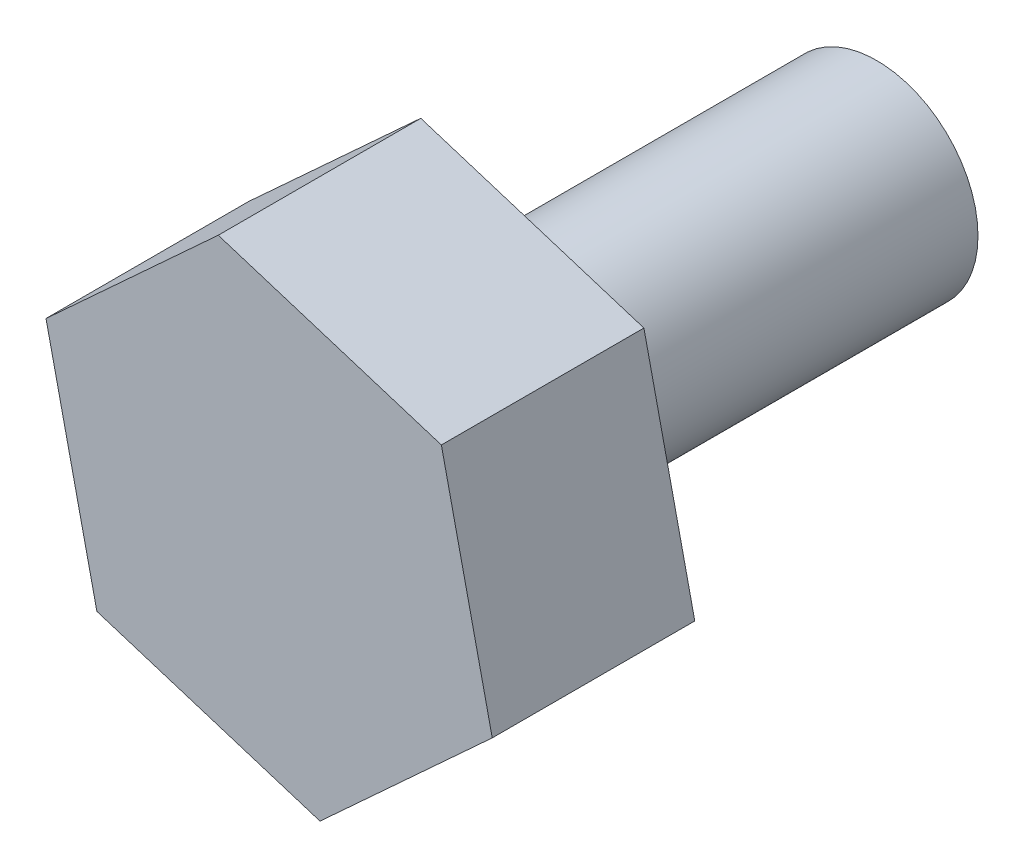
SolidWorks part; units mm, degrees
ref_plane "前视基准面" through (0, 0, 0) normal (0, 0, 1) x (1, 0, 0)
ref_plane "上视基准面" through (0, 0, 0) normal (0, 1, 0) x (1, 0, 0)
ref_plane "右视基准面" through (0, 0, 0) normal (1, 0, 0) x (0, 0, -1)
sketch "草图1" plane through (0, 0, 0) normal (0, 0, 1) x (1, 0, 0)
  line L1 (0.5025, -2.2541) -> (2.2033, -0.6919)
  line L2 (2.2033, -0.6919) -> (1.7008, 1.5622)
  line L3 (1.7008, 1.5622) -> (-0.5025, 2.2541)
  line L4 (-0.5025, 2.2541) -> (-2.2033, 0.6919)
  line L5 (-2.2033, 0.6919) -> (-1.7008, -1.5622)
  line L6 (-1.7008, -1.5622) -> (0.5025, -2.2541)
  circle A0 centre (0, 0) radius 2 construction
  dimension "D1" = 4
extrude "凸台-拉伸1" add sketch "草图1" along normal blind 2
sketch "草图2" plane through (0, 0, 0) normal (0, 0, -1) x (-1, 0, 0)
  circle A0 centre (0, 0) radius 1
extrude "凸台-拉伸2" add sketch "草图2" along normal blind 4
